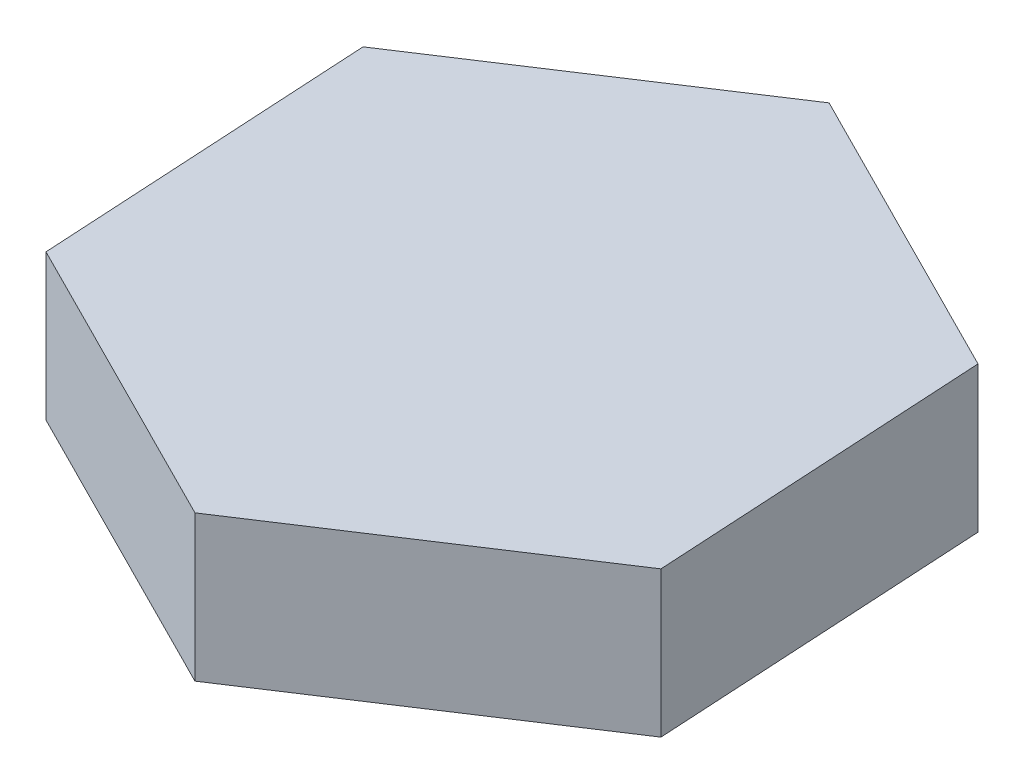
SolidWorks part; units mm, degrees
ref_plane "Front Plane" through (0, 0, 0) normal (0, 0, 1) x (1, 0, 0)
ref_plane "Top Plane" through (0, 0, 0) normal (0, 1, 0) x (1, 0, 0)
ref_plane "Right Plane" through (0, 0, 0) normal (1, 0, 0) x (0, 0, -1)
sketch "Sketch1" plane through (0, 0, 0) normal (0, 1, 0) x (1, 0, 0)
  line L1 (73.5949, 48.2256) -> (-4.9672, 87.8479)
  line L2 (-4.9672, 87.8479) -> (-78.5621, 39.6222)
  line L3 (-78.5621, 39.6222) -> (-73.5949, -48.2256)
  line L4 (-73.5949, -48.2256) -> (4.9672, -87.8479)
  line L5 (4.9672, -87.8479) -> (78.5621, -39.6222)
  line L6 (78.5621, -39.6222) -> (73.5949, 48.2256)
  circle A0 centre (0, 0) radius 76.2 construction
  dimension "D1" = 76.2
extrude "Boss-Extrude1" add sketch "Sketch1" along normal blind 38.1
sketch "Sketch2" plane through (0, 0, 0) normal (0, -1, 0) x (1, 0, 0)
  circle A0 centre (0, 0) radius 12.7
extrude "Cut-Extrude1" cut sketch "Sketch2" against normal blind 12.7
